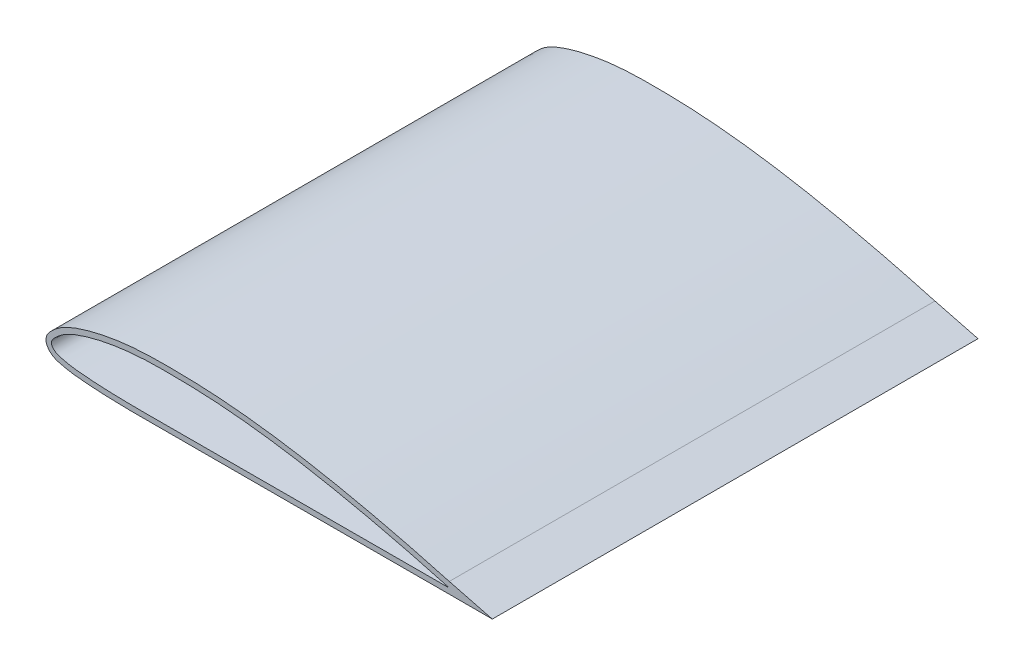
SolidWorks part; units mm, degrees
ref_plane "Front Plane" through (0, 0, 0) normal (0, 0, 1) x (1, 0, 0)
ref_plane "Top Plane" through (0, 0, 0) normal (0, 1, 0) x (1, 0, 0)
ref_plane "Right Plane" through (0, 0, 0) normal (1, 0, 0) x (0, 0, -1)
curve "Curve1"
  spline degree 3 poles (1, 0.0006, 0) (0.9967, 0.0014, 0) (0.99, 0.003, 0) (0.98, 0.0053, 0) (0.97, 0.0077, 0) (0.9567, 0.0108, 0) (0.94, 0.0146, 0) (0.92, 0.0191, 0) (0.9, 0.0235, 0) (0.88, 0.0278, 0) (0.86, 0.032, 0) (0.84, 0.0361, 0) (0.82, 0.04, 0) (0.8, 0.0439, 0) (0.78, 0.0476, 0) (0.76, 0.0513, 0) (0.74, 0.0548, 0) (0.72, 0.0582, 0) (0.7, 0.0615, 0) (0.68, 0.0646, 0) (0.66, 0.0676, 0) (0.64, 0.0705, 0) (0.62, 0.0732, 0) (0.6, 0.0758, 0) (0.58, 0.0782, 0) (0.56, 0.0804, 0) (0.54, 0.0824, 0) (0.52, 0.0842, 0) (0.5, 0.0859, 0) (0.48, 0.0874, 0) (0.46, 0.0887, 0) (0.44, 0.0898, 0) (0.42, 0.0906, 0) (0.4, 0.0912, 0) (0.38, 0.0916, 0) (0.36, 0.0917, 0) (0.34, 0.0915, 0) (0.32, 0.0912, 0) (0.3, 0.0907, 0) (0.28, 0.09, 0) (0.26, 0.0891, 0) (0.24, 0.0879, 0) (0.22, 0.0862, 0) (0.2, 0.084, 0) (0.1799, 0.0812, 0) (0.1599, 0.0777, 0) (0.1399, 0.0735, 0) (0.1199, 0.0687, 0) (0.0999, 0.0631, 0) (0.0798, 0.0565, 0) (0.0632, 0.0502, 0) (0.0499, 0.0443, 0) (0.0398, 0.0392, 0) (0.0296, 0.033, 0) (0.0203, 0.0259, 0) (0.0132, 0.0191, 0) (0.0078, 0.0137, 0) (0.0044, 0.0097, 0) (0.0022, 0.0062, 0) (0.0011, 0.004, 0) (0.0004, 0.0021, 0) (-0.0003, -0.0007, 0) (0.0001, -0.0036, 0) (0.0011, -0.0062, 0) (0.0022, -0.0082, 0) (0.0044, -0.0111, 0) (0.0077, -0.0142, 0) (0.013, -0.0178, 0) (0.0205, -0.0207, 0) (0.03, -0.0226, 0) (0.04, -0.0246, 0) (0.05, -0.0261, 0) (0.0633, -0.0275, 0) (0.08, -0.0285, 0) (0.1, -0.0294, 0) (0.12, -0.03, 0) (0.14, -0.0303, 0) (0.16, -0.0303, 0) (0.18, -0.0301, 0) (0.2, -0.0297, 0) (0.22, -0.0292, 0) (0.24, -0.0285, 0) (0.26, -0.0278, 0) (0.28, -0.0271, 0) (0.3, -0.0263, 0) (0.32, -0.0256, 0) (0.34, -0.0248, 0) (0.36, -0.0241, 0) (0.38, -0.0234, 0) (0.4, -0.0226, 0) (0.42, -0.0219, 0) (0.44, -0.0212, 0) (0.46, -0.0204, 0) (0.48, -0.0197, 0) (0.5, -0.019, 0) (0.52, -0.0182, 0) (0.54, -0.0175, 0) (0.56, -0.0168, 0) (0.58, -0.016, 0) (0.6, -0.0153, 0) (0.62, -0.0146, 0) (0.64, -0.0138, 0) (0.66, -0.0131, 0) (0.68, -0.0124, 0) (0.7, -0.0116, 0) (0.72, -0.0109, 0) (0.74, -0.0101, 0) (0.76, -0.0094, 0) (0.78, -0.0087, 0) (0.8, -0.0079, 0) (0.82, -0.0072, 0) (0.84, -0.0065, 0) (0.86, -0.0057, 0) (0.88, -0.005, 0) (0.9, -0.0043, 0) (0.92, -0.0035, 0) (0.94, -0.0028, 0) (0.9567, -0.0022, 0) (0.97, -0.0017, 0) (0.98, -0.0013, 0) (0.99, -0.001, 0) (0.9967, -0.0007, 0) (1, -0.0006, 0) knots 0 0 0 0 0.005028 0.010055 0.015081 0.020105 0.030145 0.040174 0.050191 0.060198 0.070194 0.08018 0.090156 0.100121 0.110076 0.12002 0.129954 0.139879 0.149793 0.159699 0.169594 0.17948 0.189355 0.199219 0.209073 0.218917 0.228751 0.238577 0.248396 0.258207 0.268012 0.277811 0.287604 0.297393 0.307179 0.316964 0.326749 0.336535 0.346322 0.356113 0.365908 0.375711 0.385531 0.395376 0.405259 0.415192 0.425184 0.435248 0.445412 0.455711 0.466191 0.471552 0.477055 0.482787 0.488946 0.494316 0.497126 0.500187 0.502001 0.503128 0.50385 0.50502 0.507318 0.507987 0.509024 0.510668 0.513358 0.515716 0.519949 0.524973 0.529954 0.534903 0.539824 0.54963 0.559425 0.569214 0.579 0.588784 0.59857 0.608356 0.618144 0.627933 0.637724 0.647515 0.657307 0.667099 0.67689 0.686681 0.696472 0.706263 0.716054 0.725846 0.735637 0.745428 0.755219 0.765011 0.774802 0.784593 0.794384 0.804176 0.813967 0.823758 0.833549 0.84334 0.853132 0.862923 0.872714 0.882505 0.892297 0.902088 0.911879 0.92167 0.931461 0.941253 0.951044 0.960835 0.970626 0.980418 0.985313 0.990209 0.995104 1 1 1 1
sketch "Sketch2" plane through (0, 0, 0) normal (0, 0, 1) x (1, 0, 0)
  line L0 (1, -0.0006) -> (-111.2433, -0.0006) construction
  line L1 (1.0061, 0.1754) -> (1, -0.0006)
  line L3 (1.5352, 2.1042) -> (17.4923, -2.0006)
  line L4 (1.0038, -2.0006) -> (17.4923, -2.0006)
  spline S0 degree 1 poles (1.5352, 2.1042) (1.0038, -2.0006) knots 0 0 1 1 construction
  spline S1 degree 3 poles (1.0061, 0.1754) (-0.9358, 0.7081) (-3.8475, 1.5069) (-8.7039, 2.8051) (-14.5294, 4.3114) (-20.3656, 5.749) (-27.1741, 7.349) (-33.9781, 8.8726) (-44.6779, 11.0739) (-57.3308, 13.3728) (-71.0095, 15.2439) (-80.7996, 16.1817) (-89.6088, 16.7577) (-95.4883, 16.9494) (-102.3503, 17.0132) (-107.258, 17.0037) (-112.1692, 16.8306) (-117.0923, 16.4612) (-121.0358, 15.9731) (-125.9769, 15.1312) (-129.9439, 14.2596) (-133.8889, 13.1136) (-136.8933, 12.0983) (-139.3897, 11.029) (-141.3837, 9.9199) (-142.7986, 8.9179) (-143.8683, 7.9575) (-144.6863, 7.1841) (-145.2085, 6.616) (-145.5978, 6.0643) (-145.813, 5.6279) (-145.9496, 5.1105) (-145.9171, 4.6811) (-145.7813, 4.3037) (-145.6317, 4.0021) (-145.3221, 3.5593) (-144.843, 3.0846) (-144.0891, 2.535) (-143.0082, 2.0734) (-141.6202, 1.743) (-140.1624, 1.3998) (-138.7, 1.1241) (-136.7482, 0.848) (-134.3019, 0.6215) (-131.3684, 0.3793) (-125.498, 0.0064) (-115.6953, -0.2455) (-101.9687, -0.1771) (-89.2206, -0.1643) (-73.5301, -0.1352) (-57.8396, -0.1062) (-42.149, -0.0778) (-31.3617, -0.0594) (-22.5358, -0.0426) (-13.7099, -0.0276) (-5.8646, -0.0127) (-0.9613, -0.0043) (1, -0.0006) knots 0 0 0 0 0.020105 0.030145 0.050191 0.08018 0.090156 0.12002 0.149793 0.199219 0.248396 0.287604 0.297393 0.336535 0.346322 0.365908 0.385531 0.395376 0.415192 0.425184 0.445412 0.455711 0.466191 0.477055 0.482787 0.488946 0.494316 0.497126 0.500187 0.502001 0.50385 0.50502 0.507318 0.507987 0.509024 0.510668 0.513358 0.515716 0.519949 0.524973 0.529954 0.534903 0.539824 0.54963 0.559425 0.569214 0.608356 0.657307 0.706263 0.735637 0.813967 0.862923 0.892297 0.92167 0.951044 0.980418 1 1 1 1
  spline S2 degree 3 poles (1.5352, 2.1042) (-1.4895, 2.9339) (-7.5374, 4.5873) (-19.713, 7.6937) (-35.0165, 11.2229) (-53.5308, 14.8273) (-69.1255, 17.0496) (-81.6696, 18.2776) (-91.1325, 18.8431) (-100.5785, 19.0321) (-108.4622, 19.0054) (-114.8231, 18.6719) (-119.6006, 18.1902) (-124.3362, 17.4725) (-128.2582, 16.6871) (-131.3815, 15.9138) (-133.7043, 15.2528) (-136.0049, 14.5197) (-138.3122, 13.6733) (-140.2222, 12.8248) (-141.7288, 12.0232) (-142.8506, 11.3324) (-143.9278, 10.5554) (-144.9341, 9.694) (-145.6675, 9.0171) (-146.3098, 8.3773) (-146.8042, 7.8185) (-147.2979, 7.1351) (-147.6734, 6.4007) (-147.8905, 5.6127) (-147.9432, 4.9253) (-147.8752, 4.2833) (-147.6837, 3.6454) (-147.4573, 3.1709) (-147.1053, 2.5935) (-146.6187, 2.0134) (-146.0045, 1.4531) (-145.3185, 0.9606) (-144.5733, 0.5667) (-143.6199, 0.1874) (-142.5078, -0.1069) (-141.3883, -0.367) (-140.1679, -0.6381) (-138.941, -0.8588) (-137.3062, -1.095) (-135.2992, -1.2986) (-132.9528, -1.4988) (-129.7876, -1.7371) (-125.8432, -1.946) (-121.1131, -2.1002) (-116.3926, -2.1785) (-111.6807, -2.2071) (-106.9759, -2.2038) (-100.7151, -2.1812) (-92.8956, -2.1673) (-83.5035, -2.1545) (-74.1141, -2.1361) (-64.7243, -2.119) (-52.2047, -2.0959) (-36.5554, -2.0685) (-17.776, -2.0342) (-5.2561, -2.0125) (1.0038, -2.0006) knots 0 0 0 0 0.03125 0.0625 0.125 0.1875 0.25 0.28125 0.3125 0.34375 0.375 0.390625 0.40625 0.421875 0.4375 0.445312 0.453125 0.460938 0.46875 0.476562 0.480469 0.484375 0.488281 0.492188 0.496094 0.498047 0.5 0.501953 0.503906 0.504883 0.505859 0.506836 0.507812 0.508789 0.509766 0.511719 0.513672 0.515625 0.517578 0.519531 0.523438 0.527344 0.53125 0.535156 0.539062 0.546875 0.554688 0.5625 0.578125 0.59375 0.609375 0.625 0.640625 0.65625 0.6875 0.71875 0.75 0.78125 0.8125 0.875 0.9375 1 1 1 1
  dimension "D1" = 2
extrude "Boss-Extrude1" add sketch "Sketch2" along normal blind 600
sketch "Sketch3" plane through (0, 0, 0) normal (0, 1, 0) x (1, 0, 0)
  line L0 (17.4923, -600) -> (17.4923, 0) construction
  line L1 (17.4923, -250) -> (-17.5077, -250)
  line L2 (17.4923, -250) -> (17.4923, -550)
  line L3 (17.4923, -550) -> (-17.5077, -550)
  line L4 (-17.5077, -250) -> (-17.5077, -550)
  line L5 (17.4923, -600) -> (1.5352, -600) construction
  dimension "D1" = 50
  dimension "D2" = 35
  dimension "D3" = 300
extrude "Cut-Extrude1" cut sketch "Sketch3" against normal through all both and the other way through all
sketch "Sketch4" plane through (0, 0, 250) normal (0, 0, 1) x (1, 0, 0)
  line L0 (-19.5077, 7.5859) -> (-19.5077, -2.0376)
  line L5 (1.0038, -2.0006) -> (17.4923, -2.0006)
  line L6 (17.4923, -2.0006) -> (1.5352, 2.1042)
  line L7 (-17.5077, 7.0986) -> (-17.5077, 5.0392)
  line L8 (1.0061, 0.1754) -> (1, -0.0006)
  line L9 (-17.5077, -0.034) -> (-17.5077, -2.034)
  line L10 (1.0038, -2.0006) -> (17.4923, -2.0006)
  line L11 (17.4923, -2.0006) -> (1.5352, 2.1042)
  spline S4 degree 3 poles (1705.8373, 2446.7365) (270.6605, -138.0042) (141.4322, -33.4204) (-348.965, 91.6981) (-756.6452, -113.4706) (-1663.9033, -2401.7199) knots -1.529399 -1.529399 -1.529399 -1.529399 0.03125 0.0625 3.50527 3.50527 3.50527 3.50527 only from (1.5352, 2.1042) to (-17.5077, 7.0986)
  spline S5 degree 3 poles (-677.6331, -746.1153) (-373.9035, 21.2592) (-182.745, 47.8094) (-8.7039, 2.8051) (88.9422, -23.2971) (179.0928, -69.3995) (528.4608, 849.7225) knots -1.751208 -1.751208 -1.751208 -1.751208 0.013518 0.033564 0.043604 1.022675 1.022675 1.022675 1.022675 only from (-17.5077, 5.0392) to (1.0061, 0.1754)
  spline S6 degree 3 poles (653.4701, 757.8135) (434.9384, -1.1432) (212.0835, 0.4014) (-294.5605, -0.5612) (-581.3001, 1.7197) (-864.1314, -532.2228) knots -1.237662 -1.237662 -1.237662 -1.237662 0.957987 0.987361 3.82084 3.82084 3.82084 3.82084 only from (1, -0.0006) to (-17.5077, -0.034)
  spline S7 degree 3 poles (-1962.248, -1932.831) (-861.8639, 1926.6685) (836.668, -1933.5632) (1940.8367, 1937.3193) knots -6.034629 -6.034629 -6.034629 -6.034629 7.947243 7.947243 7.947243 7.947243 only from (-17.5077, -2.034) to (1.0038, -2.0006)
  spline S8 degree 3 poles (1.5352, 2.1042) (-1.4895, 2.9339) (-7.5374, 4.5873) (-14.5673, 6.3809) (-18.5628, 7.3574) (-19.5077, 7.5859) knots 0 0 0 0 0.03125 0.0625 0.072172 0.072172 0.072172 0.072172
  spline S11 degree 3 poles (-19.5077, -2.0376) (-7.2191, -2.0156) (5.0698, -1.9952) (17.3582, -1.9661) knots 0.931737 0.931737 0.931737 0.931737 1.054429 1.054429 1.054429 1.054429
  dimension "D1" = 0
extrude "Boss-Extrude2" add sketch "Sketch4" along normal blind 2
sketch "Sketch5" plane through (0, 0, 550) normal (0, 0, -1) x (-1, 0, 0)
  line L4 (17.5077, 5.0392) -> (17.5077, 7.0986)
  line L5 (19.5077, -0.0375) -> (19.5077, 5.5292)
  line L6 (17.5077, -2.034) -> (17.5077, -0.034)
  line L7 (-1.5352, 2.1042) -> (-17.3582, -1.9661)
  line L8 (17.5077, 5.0392) -> (17.5077, 7.0986)
  line L10 (17.5077, -2.034) -> (17.5077, -0.034)
  line L11 (-1.5352, 2.1042) -> (-17.3582, -1.9661)
  line L13 (19.5077, -0.0375) -> (19.5077, 5.5292)
  line L14 (17.5077, -0.034) -> (19.5077, -0.0375)
  line L15 (17.5077, -0.034) -> (19.5077, -0.0375)
  arc A1 (19.5077, 5.5292) -> (17.5077, 5.0392) centre (160.7309, -575.2633) ccw
  arc A2 (19.5077, 5.5292) -> (17.5077, 5.0392) centre (160.7309, -575.2633) ccw
  spline S3 degree 3 poles (-1940.8381, 1937.3242) (-836.6768, -1933.5406) (861.8408, 1926.6186) (1962.226, -1932.7537) knots -6.008856 -6.008856 -6.008856 -6.008856 7.972928 7.972928 7.972928 7.972928 only from (-1.0038, -2.0006) to (17.5077, -2.034)
  spline S4 degree 3 poles (-1945.3885, 1953.3321) (-843.0686, -1938.094) (855.0252, 1919.8608) (1957.0695, -1914.7401) knots -5.912041 -5.912041 -5.912041 -5.912041 8.067143 8.067143 8.067143 8.067143 only from (-17.3582, -1.9661) to (-1.0038, -2.0006)
  spline S5 degree 3 poles (1663.9028, -2401.7186) (756.6451, -113.4705) (348.965, 91.6981) (-141.4314, -33.4202) (-270.6591, -138.0031) (-1705.8146, 2446.6955) knots -3.439924 -3.439924 -3.439924 -3.439924 0.002845 0.034095 1.594735 1.594735 1.594735 1.594735 only from (17.5077, 7.0986) to (-1.5352, 2.1042)
  spline S6 degree 3 poles (-1.0038, -2.0006) (5.1667, -2.0123) (11.3372, -2.023) (17.5077, -2.034) knots 0.938393 0.938393 0.938393 0.938393 1 1 1 1
  spline S7 degree 3 poles (-17.3582, -1.9661) (-11.9068, -1.979) (-6.4553, -1.9902) (-1.0038, -2.0006) knots 1 1 1 1 1.054429 1.054429 1.054429 1.054429
  spline S8 degree 3 poles (17.5077, 7.0986) (17.23, 7.0304) (13.9023, 6.2112) (7.5374, 4.5873) (1.4895, 2.9339) (-1.5352, 2.1042) knots 0 0 0 0 0.002845 0.034095 0.065345 0.065345 0.065345 0.065345
  dimension "D1" = 0
extrude "Boss-Extrude3" add sketch "Sketch5" along normal blind 2
sketch "Sketch6" plane through (0, 0, 548) normal (0, 0, -1) x (-1, 0, 0)
  line L1 (17.5077, 5.0392) -> (17.5077, -0.034)
  line L5 (-1.5352, 2.1042) -> (-17.3582, -1.9661)
  line L6 (17.5077, -2.034) -> (17.5077, -0.034)
  line L7 (17.5077, -0.034) -> (19.5077, -0.0375)
  line L8 (19.5077, -0.0375) -> (19.5077, 5.5292)
  line L9 (17.5077, 5.0392) -> (17.5077, 7.0986)
  line L12 (17.5077, -0.034) -> (19.5077, -0.0375)
  line L13 (19.5077, -0.0375) -> (19.5077, 5.5292)
  arc A1 (19.5077, 5.5292) -> (17.5077, 5.0392) centre (160.7308, -575.2629) ccw
  arc A2 (19.5077, 5.5292) -> (17.5077, 5.0392) centre (160.7308, -575.2629) ccw
  spline S3 degree 3 poles (819.3611, -590.4222) (457.5352, 0.186) (220.6989, 58.9727) (-93.6031, -21.2174) (-188.4793, -79.6711) (-698.2346, 719.4129) knots -1.188424 -1.188424 -1.188424 -1.188424 0.9375 0.96875 2.038361 2.038361 2.038361 2.038361 only from (17.5077, 7.0986) to (-1.5352, 2.1042)
  spline S4 degree 3 poles (-991.8622, 222.4035) (-357.2267, -215.0257) (342.8581, 202.4116) (979.0995, -200.4718) knots -2.440827 -2.440827 -2.440827 -2.440827 4.226253 4.226253 4.226253 4.226253 only from (-17.3582, -1.9661) to (-1.0038, -2.0006)
  spline S5 degree 3 poles (-977.6684, 212.7694) (-341.358, -212.4888) (359.582, 206.5154) (995.4272, -211.0013) knots -3.303776 -3.303776 -3.303776 -3.303776 3.37072 3.37072 3.37072 3.37072 only from (-1.0038, -2.0006) to (17.5077, -2.034)
  dimension "D1" = 0
extrude "Boss-Extrude4" add sketch "Sketch6" along normal up to surface (296 mm away)
sketch "Sketch7" plane through (0, 0, 0) normal (0, 1, 0) x (1, 0, 0)
  line L0 (-147.9233, 0) -> (-147.9233, -600) construction
  line L1 (-102.9233, -388) -> (-62.9233, -388)
  line L2 (-102.9233, -388) -> (-102.9233, -428)
  line L3 (-102.9233, -428) -> (-62.9233, -428)
  line L4 (-62.9233, -388) -> (-62.9233, -428)
  line L5 (1.5352, -548) -> (-17.5077, -548) construction
  dimension "D1" = 40
  dimension "D2" = 40
  dimension "D3" = 45
  dimension "D4" = 120
extrude "Cut-Extrude2" cut sketch "Sketch7" against normal through all
fillet "Fillet1" radius 5 4 edges at (-62.9233, -1.1157, 428) (-62.9233, -1.1157, 388) (-102.9233, -1.1898, 388) (-102.9233, -1.1898, 428)
ref_plane "Plane1" through (-284.5077, 10.3681, -35) normal (0, 1, 0) x (0, 0, 1)
sketch "Sketch8" plane through (-284.5077, 10.3681, -35) normal (0, 1, 0) x (0, 0, 1)
  line L0 (428, 181.5843) -> (458, 181.5843) construction
  line L1 (463, 216.5843) -> (463, 186.5843) construction
  line L2 (458, 221.5843) -> (428, 221.5843) construction
  line L3 (423, 186.5843) -> (423, 216.5843) construction
  line L4 (428, 181.5843) -> (458, 181.5843)
  line L5 (463, 216.5843) -> (463, 186.5843)
  line L6 (458, 221.5843) -> (428, 221.5843)
  line L7 (423, 186.5843) -> (423, 216.5843)
  arc A0 (458, 181.5843) -> (463, 186.5843) centre (458, 186.5843) ccw construction
  arc A1 (463, 216.5843) -> (458, 221.5843) centre (458, 216.5843) ccw construction
  arc A2 (428, 221.5843) -> (423, 216.5843) centre (428, 216.5843) ccw construction
  arc A3 (423, 186.5843) -> (428, 181.5843) centre (428, 186.5843) ccw construction
  arc A4 (458, 181.5843) -> (463, 186.5843) centre (458, 186.5843) ccw
  arc A5 (463, 216.5843) -> (458, 221.5843) centre (458, 216.5843) ccw
  arc A6 (428, 221.5843) -> (423, 216.5843) centre (428, 216.5843) ccw
  arc A7 (423, 186.5843) -> (428, 181.5843) centre (428, 186.5843) ccw
extrude "Boss-Extrude5" add sketch "Sketch8" along normal up to surface (4.4093 mm away)
ref_plane "Plane2" through (0, 0, 200) normal (0, 0, -1) x (-1, 0, 0)
split "Split1" trim tools "Plane2" bodies to split 107 resulting bodies 110
sketch "Sketch9" plane through (0, 0, 0) normal (0, 0, -1) x (-1, 0, 0)
  line L2 (-1.5352, 2.1042) -> (-17.4923, -2.0006)
  line L3 (-17.4923, -2.0006) -> (-1.0038, -2.0006)
  line L4 (-1.5352, 2.1042) -> (-17.4923, -2.0006)
  line L5 (-17.4923, -2.0006) -> (-1.0038, -2.0006)
  spline S1 degree 3 poles (-2171.7973, 2910.1982) (-1591.1801, -4.1463) (-779.8572, -0.5762) (36.5554, -2.0685) (52.2047, -2.0959) (64.7243, -2.119) (74.1141, -2.1361) (83.5035, -2.1545) (92.8956, -2.1673) (100.7151, -2.1812) (106.9759, -2.2038) (111.6807, -2.2071) (116.3926, -2.1785) (121.1131, -2.1002) (125.8432, -1.946) (129.7876, -1.7371) (132.9528, -1.4988) (135.2992, -1.2986) (137.3062, -1.095) (138.941, -0.8588) (140.1679, -0.6381) (141.3883, -0.367) (142.5078, -0.1069) (143.6199, 0.1874) (144.5733, 0.5667) (145.3185, 0.9606) (146.0045, 1.4531) (146.6187, 2.0134) (147.1053, 2.5935) (147.4573, 3.1709) (147.6837, 3.6454) (147.8752, 4.2833) (147.9432, 4.9253) (147.8905, 5.6127) (147.6734, 6.4007) (147.2979, 7.1351) (146.8042, 7.8185) (146.3098, 8.3773) (145.6675, 9.0171) (144.9341, 9.694) (143.9278, 10.5554) (142.8506, 11.3324) (141.7288, 12.0232) (140.2222, 12.8248) (138.3122, 13.6733) (136.0049, 14.5197) (133.7043, 15.2528) (131.3815, 15.9138) (128.2582, 16.6871) (124.3362, 17.4725) (119.6006, 18.1902) (114.8231, 18.6719) (108.4622, 19.0054) (100.5785, 19.0321) (91.1325, 18.8431) (81.6696, 18.2776) (69.1255, 17.0496) (53.5308, 14.8273) (35.0165, 11.2229) (19.713, 7.6937) (-156.9168, -37.3711) (-296.2132, -159.5408) (-2186.5508, 3323.1595) knots -7.963834 -7.963834 -7.963834 -7.963834 0.0625 0.125 0.1875 0.21875 0.25 0.28125 0.3125 0.34375 0.359375 0.375 0.390625 0.40625 0.421875 0.4375 0.445312 0.453125 0.460938 0.464844 0.46875 0.472656 0.476562 0.480469 0.482422 0.484375 0.486328 0.488281 0.490234 0.491211 0.492188 0.493164 0.494141 0.495117 0.496094 0.498047 0.5 0.501953 0.503906 0.507812 0.511719 0.515625 0.519531 0.523438 0.53125 0.539062 0.546875 0.554688 0.5625 0.578125 0.59375 0.609375 0.625 0.65625 0.6875 0.71875 0.75 0.8125 0.875 0.9375 0.96875 2.688371 2.688371 2.688371 2.688371 only from (-1.0038, -2.0006) to (-1.5352, 2.1042)
  spline S2 degree 3 poles (-1.0038, -2.0006) (5.2561, -2.0125) (17.776, -2.0342) (36.5554, -2.0685) (52.2047, -2.0959) (64.7243, -2.119) (74.1141, -2.1361) (83.5035, -2.1545) (92.8956, -2.1673) (100.7151, -2.1812) (106.9759, -2.2038) (111.6807, -2.2071) (116.3926, -2.1785) (121.1131, -2.1002) (125.8432, -1.946) (129.7876, -1.7371) (132.9528, -1.4988) (135.2992, -1.2986) (137.3062, -1.095) (138.941, -0.8588) (140.1679, -0.6381) (141.3883, -0.367) (142.5078, -0.1069) (143.6199, 0.1874) (144.5733, 0.5667) (145.3185, 0.9606) (146.0045, 1.4531) (146.6187, 2.0134) (147.1053, 2.5935) (147.4573, 3.1709) (147.6837, 3.6454) (147.8752, 4.2833) (147.9432, 4.9253) (147.8905, 5.6127) (147.6734, 6.4007) (147.2979, 7.1351) (146.8042, 7.8185) (146.3098, 8.3773) (145.6675, 9.0171) (144.9341, 9.694) (143.9278, 10.5554) (142.8506, 11.3324) (141.7288, 12.0232) (140.2222, 12.8248) (138.3122, 13.6733) (136.0049, 14.5197) (133.7043, 15.2528) (131.3815, 15.9138) (128.2582, 16.6871) (124.3362, 17.4725) (119.6006, 18.1902) (114.8231, 18.6719) (108.4622, 19.0054) (100.5785, 19.0321) (91.1325, 18.8431) (81.6696, 18.2776) (69.1255, 17.0496) (53.5308, 14.8273) (35.0165, 11.2229) (19.713, 7.6937) (7.5374, 4.5873) (1.4895, 2.9339) (-1.5352, 2.1042) knots 0 0 0 0 0.0625 0.125 0.1875 0.21875 0.25 0.28125 0.3125 0.34375 0.359375 0.375 0.390625 0.40625 0.421875 0.4375 0.445312 0.453125 0.460938 0.464844 0.46875 0.472656 0.476562 0.480469 0.482422 0.484375 0.486328 0.488281 0.490234 0.491211 0.492188 0.493164 0.494141 0.495117 0.496094 0.498047 0.5 0.501953 0.503906 0.507812 0.511719 0.515625 0.519531 0.523438 0.53125 0.539062 0.546875 0.554688 0.5625 0.578125 0.59375 0.609375 0.625 0.65625 0.6875 0.71875 0.75 0.8125 0.875 0.9375 0.96875 1 1 1 1
  dimension "D1" = 0
extrude "Cut-Extrude3" cut sketch "Sketch9" against normal blind 20
